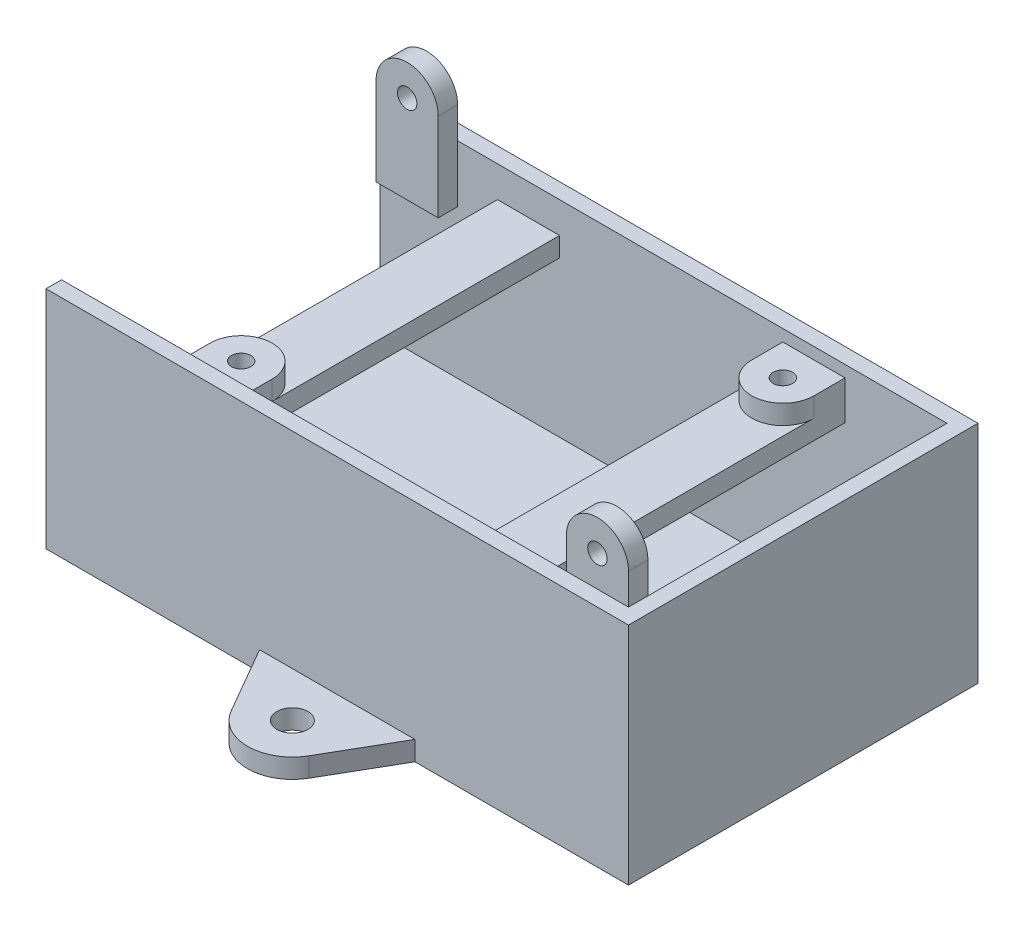
SolidWorks part; units mm, degrees
ref_plane "Front Plane" through (0, 0, 0) normal (0, 0, 1) x (1, 0, 0)
ref_plane "Top Plane" through (0, 0, 0) normal (0, 1, 0) x (1, 0, 0)
ref_plane "Right Plane" through (0, 0, 0) normal (1, 0, 0) x (0, 0, -1)
sketch "Sketch1" plane through (0, 0, 0) normal (0, 1, 0) x (1, 0, 0)
  line L1 (-37.5, -22.5) -> (37.5, -22.5)
  line L2 (-37.5, -22.5) -> (-37.5, 22.5)
  line L3 (-37.5, 22.5) -> (37.5, 22.5)
  line L4 (37.5, -22.5) -> (37.5, 22.5)
  line L5 (-37.5, -22.5) -> (37.5, 22.5) construction
  line L6 (-37.5, 22.5) -> (37.5, -22.5) construction
  point P0 (0, 0)
  dimension "D1" = 75
  dimension "D2" = 45
extrude "Boss-Extrude1" add sketch "Sketch1" along normal blind 2.5
sketch "Sketch2" plane through (0, 2.5, 0) normal (0, 1, 0) x (1, 0, 0)
  line L0 (-37.5, 22.5) -> (37.5, 22.5)
  line L1 (37.5, 22.5) -> (37.5, -22.5)
  line L2 (37.5, -22.5) -> (-37.5, -22.5)
  line L3 (-37.5, -22.5) -> (-37.5, 22.5)
  line L5 (-35.5, -20.5) -> (35.5, -20.5)
  line L6 (-35.5, -20.5) -> (-35.5, 20.5)
  line L7 (-35.5, 20.5) -> (35.5, 20.5)
  line L8 (35.5, -20.5) -> (35.5, 20.5)
  line L9 (-35.5, -20.5) -> (35.5, 20.5) construction
  line L10 (-35.5, 20.5) -> (35.5, -20.5) construction
  point P8 (0, 0)
  dimension "D1" = 2
  dimension "D2" = 2
extrude "Boss-Extrude2" add sketch "Sketch2" along normal blind 20 contours L3 L0 L1 L2 | L6 L5 L8 L7
sketch "Sketch4" plane through (-37.5, 0, 0) normal (-1, 0, 0) x (0, 0, 1)
  line L0 (22.5, 22.5) -> (-22.5, 22.5) construction
  line L1 (-20.5, 2.5) -> (20.5, 2.5)
  line L2 (-20.5, 2.5) -> (-20.5, 22.5)
  line L3 (-20.5, 22.5) -> (20.5, 22.5)
  line L4 (20.5, 2.5) -> (20.5, 22.5)
  line L5 (-20.5, 2.5) -> (20.5, 22.5) construction
  line L6 (-20.5, 22.5) -> (20.5, 2.5) construction
  line L7 (20.5, 2.5) -> (-20.5, 2.5) construction
  point P4 (0, 12.5)
  point P5 (0, 0)
  point P7 (0, 0)
extrude "Cut-Extrude1" cut sketch "Sketch4" against normal up to surface (2 mm away) up to face at (-35.5, 12.5, 0)
sketch "Sketch5" plane through (0, 22.5, 0) normal (0, 1, 0) x (1, 0, 0)
  line L0 (-37.5, 22.5) -> (37.5, 22.5) construction
  line L1 (-22.375, 22.5) -> (-14.375, 22.5)
  line L2 (-22.375, 22.5) -> (-22.375, -22.5)
  line L3 (-22.375, -22.5) -> (-14.375, -22.5)
  line L4 (-14.375, 22.5) -> (-14.375, -22.5)
  line L5 (-22.375, 22.5) -> (-14.375, -22.5) construction
  line L6 (-22.375, -22.5) -> (-14.375, 22.5) construction
  line L7 (37.5, -22.5) -> (-37.5, -22.5) construction
  line L9 (22.375, -22.5) -> (14.375, -22.5)
  line L10 (22.375, -22.5) -> (22.375, 22.5)
  line L11 (22.375, 22.5) -> (14.375, 22.5)
  line L12 (14.375, -22.5) -> (14.375, 22.5)
  line L13 (22.375, -22.5) -> (14.375, 22.5) construction
  line L14 (22.375, 22.5) -> (14.375, -22.5) construction
  line L15 (0, 0) -> (18.375, 0) construction
  line L16 (0, 0) -> (-18.375, 0) construction
  point P4 (-18.375, 0)
  point P13 (18.375, 0)
  dimension "D1" = 8
  dimension "D2" = 8
  dimension "D3" = 36.75
extrude "Boss-Extrude4" add sketch "Sketch5" along normal blind 2.5
sketch "Sketch7" plane through (0, 22.5, 0) normal (0, 1, 0) x (1, 0, 0)
  line L0 (-37.5, 22.5) -> (37.5, 22.5)
  line L1 (37.5, 22.5) -> (37.5, -22.5)
  line L2 (37.5, -22.5) -> (-37.5, -22.5)
  line L3 (-37.5, -22.5) -> (-37.5, -20.5)
  line L4 (-37.5, -20.5) -> (35.5, -20.5)
  line L5 (35.5, -20.5) -> (35.5, 20.5)
  line L6 (35.5, 20.5) -> (-37.5, 20.5)
  line L7 (-37.5, 20.5) -> (-37.5, 22.5)
extrude "Boss-Extrude5" add sketch "Sketch7" along normal blind 6.5
sketch "Sketch8" plane through (0, 25, 0) normal (0, 1, 0) x (1, 0, 0)
  line L0 (-22.375, -20.5) -> (-14.375, -20.5)
  line L1 (-14.375, -20.5) -> (-14.375, -16.5)
  line L2 (-14.375, -20.5) -> (-14.375, 20.5) construction
  line L3 (-22.375, -20.5) -> (-22.375, -16.5)
  line L4 (-22.375, 20.5) -> (-22.375, -20.5) construction
  line L7 (22.375, -20.5) -> (22.375, 20.5) construction
  line L9 (14.375, 20.5) -> (14.375, -20.5) construction
  line L10 (14.375, 16.5) -> (14.375, 20.5)
  line L11 (14.375, 20.5) -> (22.375, 20.5)
  line L12 (22.375, 20.5) -> (22.375, 16.5)
  arc A0 (-14.375, -16.5) -> (-22.375, -16.5) centre (-18.375, -16.5) ccw
  arc A1 (14.375, 16.5) -> (22.375, 16.5) centre (18.375, 16.5) ccw
  dimension "D1" = 4
extrude "Boss-Extrude6" add sketch "Sketch8" along normal blind 2.5
sketch "Sketch9" plane through (0, 27.5, 0) normal (0, 1, 0) x (1, 0, 0)
  line L0 (37.5, -22.5) -> (37.5, 22.5) construction
  circle A0 centre (-18.375, -16.5) radius 1.25
  circle A1 centre (18.375, 16.5) radius 1.25
  dimension "D1" = 2.5
  dimension "D2" = 2.5
extrude "Cut-Extrude2" cut sketch "Sketch9" against normal up to surface (5 mm away) up to face at (-18.375, 22.5, 0)
sketch "Sketch12" plane through (0, 0, 20.5) normal (0, 0, -1) x (-1, 0, 0)
  line L0 (-35.5, 22.5) -> (-27.5, 22.5)
  line L1 (-35.5, 29) -> (-35.5, 2.5) construction
  line L2 (-27.5, 22.5) -> (-27.5, 29)
  line L3 (-35.5, 29) -> (37.5, 29) construction
  line L4 (-27.5, 29) -> (-27.5, 33)
  line L7 (-35.5, 33) -> (-35.5, 22.5)
  arc A0 (-35.5, 33) -> (-27.5, 33) centre (-31.5, 33) cw
  dimension "D1" = 8
  dimension "D2" = 4
extrude "Boss-Extrude7" add sketch "Sketch12" along normal blind 2.5
sketch "Sketch13" plane through (0, 0, -20.5) normal (0, 0, 1) x (1, 0, 0)
  line L0 (-35.5, 29) -> (-35.5, 21.655)
  line L1 (-37.5, 29) -> (35.5, 29) construction
  line L2 (-35.5, 21.655) -> (-27.5, 21.655)
  line L3 (-27.5, 21.655) -> (-27.5, 29)
  line L4 (-37.5, 29) -> (-37.5, 2.5) construction
  line L5 (-35.5, 29) -> (-35.5, 33)
  line L6 (-27.5, 29) -> (-27.5, 33)
  arc A0 (-35.5, 33) -> (-27.5, 33) centre (-31.5, 33) cw
  dimension "D1" = 2
  dimension "D2" = 8
  dimension "D3" = 4
extrude "Boss-Extrude8" add sketch "Sketch13" along normal blind 2.5
sketch "Sketch14" plane through (0, 0, -20.5) normal (0, 0, -1) x (-1, 0, 0)
  circle A0 centre (31.5, 33) radius 1.25
  dimension "D1" = 2.5
extrude "Cut-Extrude3" cut sketch "Sketch14" against normal up to surface (2.5 mm away) up to face at (-31.5, 28.3275, -18)
sketch "Sketch15" plane through (0, 0, 18) normal (0, 0, -1) x (-1, 0, 0)
  circle A0 centre (-31.5, 33) radius 1.25
  dimension "D1" = 2.5
extrude "Cut-Extrude4" cut sketch "Sketch15" against normal up to surface (2.5 mm away) up to face at (31.5, 32, 20.5)
sketch "Sketch16" plane through (0, 0, 0) normal (0, -1, 0) x (-1, 0, 0)
  line L6 (-10, -22.5) -> (10, -22.5)
  line L15 (37.5, -22.5) -> (-37.5, -22.5) construction
  line L16 (-10, -22.5) -> (-5, -31.1603)
  line L18 (5, -31.1603) -> (10, -22.5)
  arc A0 (-5, -31.1603) -> (5, -31.1603) centre (0, -28.2735) ccw
  point P5 (0, -22.5)
  dimension "D1" = 20
  dimension "D2" = 60
  dimension "D3" = 60
  dimension "D4" = 10
extrude "Boss-Extrude9" add sketch "Sketch16" against normal blind 2.5 separate body
sketch "Sketch20" plane through (0, 0, 0) normal (0, -1, 0) x (1, 0, 0)
  circle A0 centre (0, 28.2735) radius 2
  dimension "D1" = 4
extrude "Cut-Extrude6" cut sketch "Sketch20" against normal up to surface (2.5 mm away) up to face at (0, 2.5, 27.5518)
mirror "Mirror2" about plane through (0, 0, 0) normal (0, 0, 1) of bodies 122 120
equation "\"ˇ5\"=5.24808"
